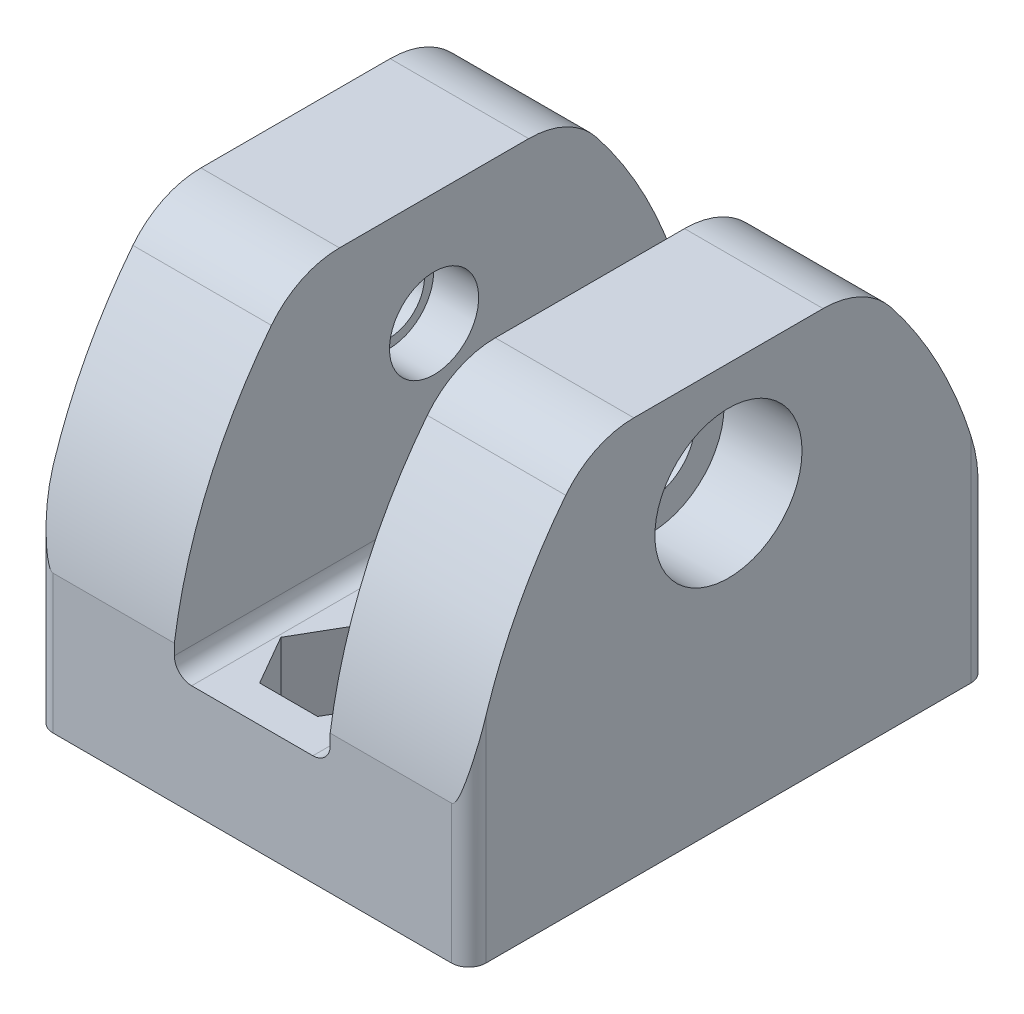
SolidWorks part; units mm, degrees
ref_plane "Alzado" through (0, 0, 0) normal (0, 0, 1) x (1, 0, 0)
ref_plane "Planta" through (0, 0, 0) normal (0, 1, 0) x (1, 0, 0)
ref_plane "Vista lateral" through (0, 0, 0) normal (1, 0, 0) x (0, 0, -1)
sketch "Croquis1" plane through (0, 0, 0) normal (0, 1, 0) x (1, 0, 0)
  line L0 (12.5, 30) -> (12.5, 0) construction
  line L1 (0, 0) -> (25, 0)
  line L2 (0, 0) -> (0, 30)
  line L3 (0, 30) -> (25, 30)
  line L4 (25, 0) -> (25, 30)
  circle A0 centre (12.5, 25) radius 1.55
  circle A1 centre (12.5, 5) radius 1.55
  dimension "D3" = 20
  dimension "D4" = 3.1
  dimension "D1" = 25
  dimension "D2" = 30
  dimension "D5" = 5
extrude "Saliente-Extruir1" add sketch "Croquis1" along normal blind 23
sketch "Croquis2" plane through (0, 0, -30) normal (0, 0, -1) x (-1, 0, 0)
  line L0 (-25, 23) -> (0, 23) construction
  line L1 (-8, 23) -> (-17, 23)
  line L2 (-8, 23) -> (-8, 6.3673)
  line L3 (-8, 6.3673) -> (-17, 6.3673)
  line L4 (-17, 23) -> (-17, 6.3673)
  line L5 (0, 23) -> (0, 0) construction
  dimension "D1" = 9
  dimension "D2" = 8
extrude "Cortar-Extruir1" cut sketch "Croquis2" against normal up to surface (30 mm away) up to face at (12.5, 11.5, 0)
sketch "Croquis3" plane through (0, 0, 0) normal (-1, 0, 0) x (0, 0, 1)
  line L0 (-15, 0) -> (-15, 23) construction
  line L1 (-30, 0) -> (0, 0) construction
  line L2 (-30, 23) -> (0, 23) construction
  circle A0 centre (-15, 16.5) radius 2.575
  dimension "D1" = 5.15
  dimension "D2" = 6.5
extrude "Cortar-Extruir2" cut sketch "Croquis3" against normal up to surface (25 mm away) up to face at (25, 11.5, -15)
sketch "Croquis4" plane through (0, 0, 0) normal (-1, 0, 0) x (0, 0, 1)
  line L1 (-14.9518, 20.5412) -> (-18.4757, 18.5623)
  line L2 (-18.4757, 18.5623) -> (-18.5238, 14.5212)
  line L3 (-18.5238, 14.5212) -> (-15.0482, 12.4588)
  line L4 (-15.0482, 12.4588) -> (-11.5243, 14.4377)
  line L5 (-11.5243, 14.4377) -> (-11.4762, 18.4788)
  line L6 (-11.4762, 18.4788) -> (-14.9518, 20.5412)
  circle A0 centre (-15, 16.5) radius 3.5 construction
  dimension "D1" = 7
extrude "Cortar-Extruir3" cut sketch "Croquis4" against normal blind 2.5
sketch "Croquis5" plane through (25, 0, 0) normal (1, 0, 0) x (0, 0, -1)
  circle A0 centre (15, 16.5) radius 4.25
  dimension "D1" = 8.5
extrude "Cortar-Extruir4" cut sketch "Croquis5" against normal blind 4.5
sketch "Croquis6" plane through (0, 6.3673, 0) normal (0, 1, 0) x (1, 0, 0)
  line L1 (15.8486, 25) -> (14.1743, 27.9)
  line L2 (14.1743, 27.9) -> (10.8257, 27.9)
  line L3 (10.8257, 27.9) -> (9.1514, 25)
  line L4 (9.1514, 25) -> (10.8257, 22.1)
  line L5 (10.8257, 22.1) -> (14.1743, 22.1)
  line L6 (14.1743, 22.1) -> (15.8486, 25)
  line L7 (15.8486, 5) -> (14.1743, 7.9)
  line L8 (14.1743, 7.9) -> (10.8257, 7.9)
  line L9 (10.8257, 7.9) -> (9.1514, 5)
  line L10 (9.1514, 5) -> (10.8257, 2.1)
  line L11 (10.8257, 2.1) -> (14.1743, 2.1)
  line L12 (14.1743, 2.1) -> (15.8486, 5)
  circle A0 centre (12.5, 25) radius 2.9 construction
  circle A1 centre (12.5, 5) radius 2.9 construction
  dimension "D1" = 5.8
  dimension "D2" = 5.8
extrude "Cortar-Extruir5" cut sketch "Croquis6" against normal blind 4.5
sketch "Croquis7" plane through (0, 0, 0) normal (-1, 0, 0) x (0, 0, 1)
  line L0 (-15, 0) -> (-15, 23) construction
  line L1 (-30, 0) -> (0, 0) construction
  line L2 (-30, 23) -> (0, 23) construction
  line L3 (-30, 23) -> (-30, 8)
  line L4 (-30, 23) -> (-30, 0) construction
  line L5 (-30, 23) -> (-22.746, 23)
  line L6 (0, 23) -> (-7.254, 23)
  line L7 (0, 23) -> (0, 8)
  circle A0 centre (-15, 17.5) radius 9.5
  arc A1 (-30, 8) -> (-22.746, 23) centre (-2.7727, 4.0869) cw
  arc A2 (0, 8) -> (-7.254, 23) centre (-27.2273, 4.0869) ccw
  line M8 (0, 0) -> (0, 23)
  line M9 (0, 23) -> (-30, 23)
  line M10 (-30, 23) -> (-30, 0)
  dimension "D1" = 19
  dimension "D2" = 8
  dimension "D3" = 5.5
extrude "Cortar-Extruir6" cut sketch "Croquis7" against normal up to surface (25 mm away) contours A1 M10 M9 | A2 M8 M9 up to face at (25, 16.5, -19.25)
fillet "Redondeo2" radius 1 2 edges at (17, 6.3673, -15) (8, 6.3673, -15)
fillet "Redondeo3" radius 1 4 edges at (25, 4, 0) (0, 4, 0) (0, 4, -30) (25, 4, -30)
fillet "Redondeo4" radius 5 4 edges at (4, 23, -22.746) (4, 23, -7.254) (21, 23, -7.254) (21, 23, -22.746)
sketch "Croquis8" plane through (2.5, 0, 0) normal (-1, 0, 0) x (0, 0, 1)
  circle A0 centre (-15, 16.5) radius 2.575 construction
  circle A1 centre (-15, 16.5) radius 2.575
  circle A2 centre (-15, 16.5) radius 2.05
  dimension "D1" = 4.1
extrude "Saliente-Extruir2" add sketch "Croquis8" against normal blind 2.9
sketch "Croquis9" plane through (2.5, 0, 0) normal (-1, 0, 0) x (0, 0, 1)
  line L6 (-11.4762, 18.4788) -> (-14.9518, 20.5412)
  line L7 (-14.9518, 20.5412) -> (-18.4757, 18.5623)
  line L8 (-18.4757, 18.5623) -> (-18.5238, 14.5212)
  line L9 (-18.5238, 14.5212) -> (-15.0482, 12.4588)
  line L10 (-15.0482, 12.4588) -> (-11.5243, 14.4377)
  line L11 (-11.5243, 14.4377) -> (-11.4762, 18.4788)
  line L12 (-11.4762, 18.4788) -> (-14.9518, 20.5412)
  line L13 (-14.9518, 20.5412) -> (-18.4757, 18.5623)
  line L14 (-18.4757, 18.5623) -> (-18.5238, 14.5212)
  line L15 (-18.5238, 14.5212) -> (-15.0482, 12.4588)
  line L16 (-15.0482, 12.4588) -> (-11.5243, 14.4377)
  line L17 (-11.5243, 14.4377) -> (-11.4762, 18.4788)
  dimension "D1" = 0
extrude "Cortar-Extruir7" cut sketch "Croquis9" against normal blind 1.5
